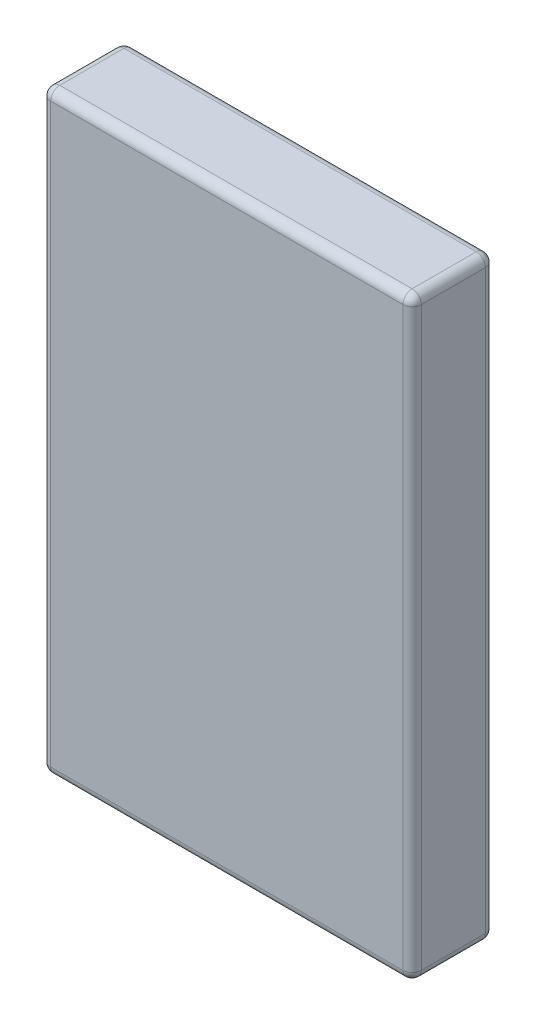
SolidWorks part; units mm, degrees
ref_plane "Front Plane" through (0, 0, 0) normal (0, 0, 1) x (1, 0, 0)
ref_plane "Top Plane" through (0, 0, 0) normal (0, 1, 0) x (1, 0, 0)
ref_plane "Right Plane" through (0, 0, 0) normal (1, 0, 0) x (0, 0, -1)
sketch "Sketch2" plane through (0, 0, 0) normal (0, 1, 0) x (1, 0, 0)
  line L1 (-81, 18) -> (81, 18)
  line L2 (-81, 18) -> (-81, -18)
  line L3 (-81, -18) -> (81, -18)
  line L4 (81, 18) -> (81, -18)
  line L5 (-81, 18) -> (81, -18) construction
  line L6 (-81, -18) -> (81, 18) construction
  point P0 (0, 0)
  dimension "D1" = 162
  dimension "D2" = 36
extrude "Boss-Extrude1" add sketch "Sketch2" along normal blind 260
fillet "Fillet1" radius 4 12 edges at (-81, 130, -18) (-81, 260, 0) (-81, 130, 18) (-81, 0, 0) (81, 0, 0) (0, 0, -18) (0, 0, 18) (81, 260, 0) (81, 130, -18) (81, 130, 18) (0, 260, -18) (0, 260, 18)
